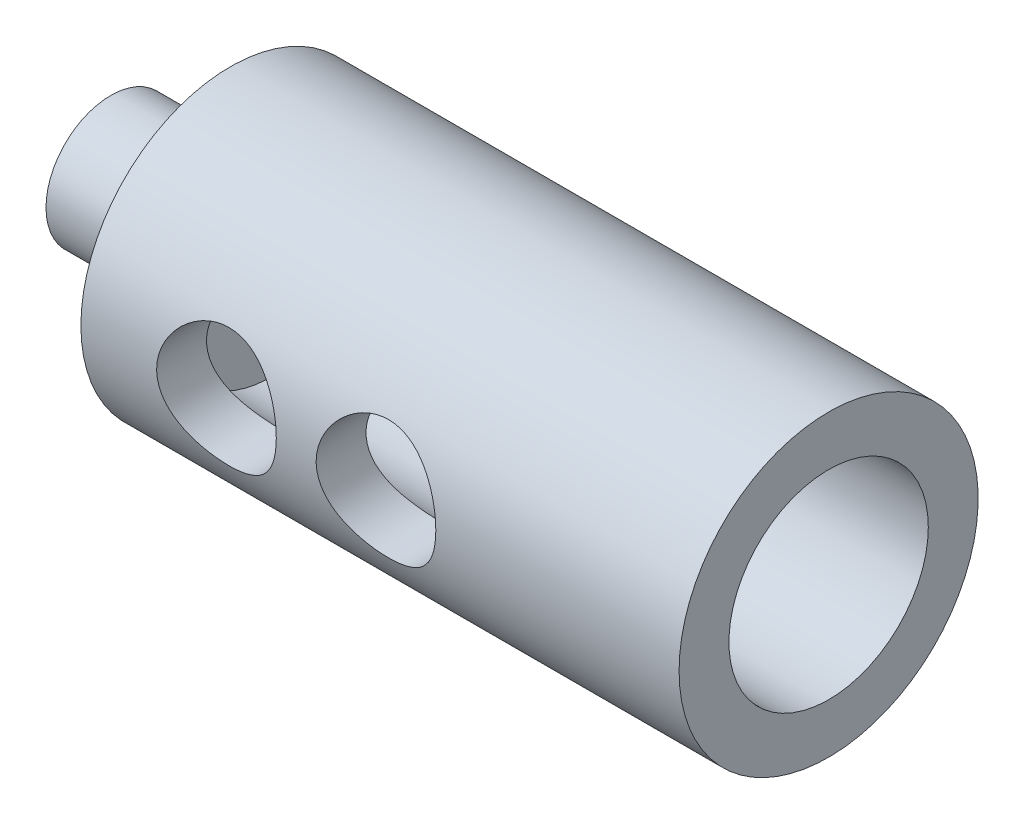
SolidWorks part; units mm, degrees
ref_plane "Front Plane" through (0, 0, 0) normal (0, 0, 1) x (1, 0, 0)
ref_plane "Top Plane" through (0, 0, 0) normal (0, 1, 0) x (1, 0, 0)
ref_plane "Right Plane" through (0, 0, 0) normal (1, 0, 0) x (0, 0, -1)
sketch "Sketch1" plane through (0, 0, 0) normal (0, 0, 1) x (1, 0, 0)
  line L0 (0, 0) -> (-6, 0)
  line L1 (0, 0) -> (0, 4.25)
  line L2 (0, 4.25) -> (30, 4.25)
  line L3 (30, 4.25) -> (30, -3.25)
  line L4 (-6, 0) -> (-6, -1.5)
  line L5 (-6, -1.5) -> (2, -1.5)
  line L6 (2, -1.5) -> (2, 0.25)
  line L7 (2, 0.25) -> (28, 0.25)
  line L8 (28, 0.25) -> (28, -3.25)
  line L9 (-6, -3.25) -> (18.0316, -3.25) construction
  line L10 (30, -3.25) -> (28, -3.25)
  line L11 (0, 4.25) -> (30, 4.25) construction
  line L12 (15, 4.25) -> (15, 8.3538) construction
  line L13 (15, 8.3538) -> (15, 0.9451) construction
  dimension "D1" = 1.5
  dimension "D3" = 4
  dimension "D4" = 2
  dimension "D5" = 2
  dimension "D2" = 7.5
  dimension "D7" = 30
  dimension "D8" = 6
revolve "Revolve2" add sketch "Sketch1" angle 360 about L9
hole_wizard "Ø6.0 (6) Diameter Hole3" positions "3DSketch5" profile "Sketch6" hole size "Ø6.0" standard "ANSI Metric" end condition through all
sketch3d "3DSketch5"
  point P0 (6.799, -3.243, 7.5)
  point P2 (14.799, -3.243, 7.5)
  dimension "D1" = 8
sketch "Sketch6" plane through (6.799, -3.243, 7.5) normal (1, 0, 0) x (0, -1, 0.0009)
  line L0 (0, 0) -> (0, 15.007)
  line L1 (0, 15.007) -> (3, 15.007)
  line L2 (3, 15.007) -> (3, 0)
  line L5 (3, 0) -> (0, 0)
  line L11 (0, -6.35) -> (0, 107.95) construction
  dimension "Thru Hole Dia." = 6
  dimension "Thru Hole Depth" = 15.007
sketch "Sketch7" plane through (30, 0, 0) normal (1, 0, 0) x (0, 0, -1)
  circle A0 centre (0, -3.25) radius 5
  dimension "D1" = 10
extrude "Cut-Extrude1" cut sketch "Sketch7" against normal blind 28
equation "\"D5@Sketch1\"=\"D4@Sketch1\""
